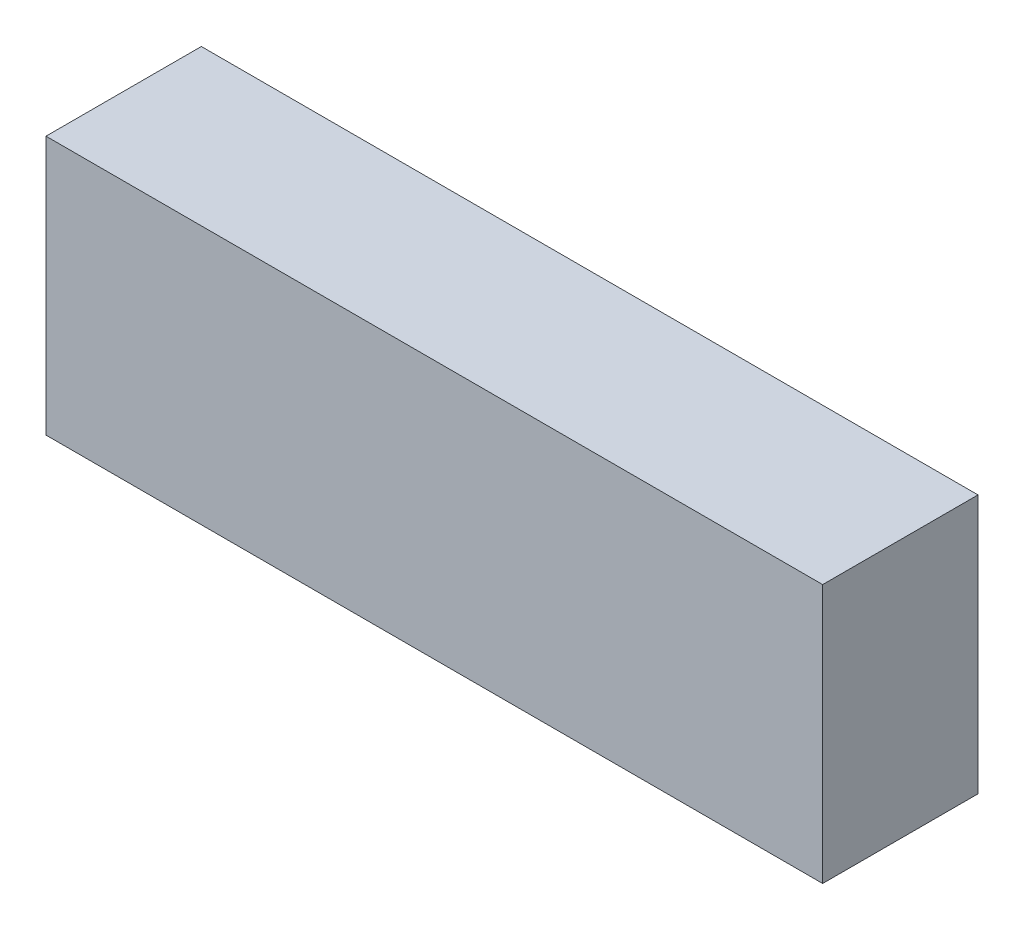
SolidWorks part; units mm, degrees
ref_plane "Front Plane" through (0, 0, 0) normal (0, 0, 1) x (1, 0, 0)
ref_plane "Top Plane" through (0, 0, 0) normal (0, 1, 0) x (1, 0, 0)
ref_plane "Right Plane" through (0, 0, 0) normal (1, 0, 0) x (0, 0, -1)
sketch "Sketch1" plane through (0, 0, 0) normal (0, 1, 0) x (1, 0, 0)
  line L1 (-75, 28.2353) -> (75, 28.2353)
  line L2 (-75, 28.2353) -> (-75, -1.7647)
  line L3 (-75, -1.7647) -> (75, -1.7647)
  line L4 (75, 28.2353) -> (75, -1.7647)
  dimension "D1" = 150
  dimension "D2" = 30
extrude "Boss-Extrude2" add sketch "Sketch1" along normal blind 50
